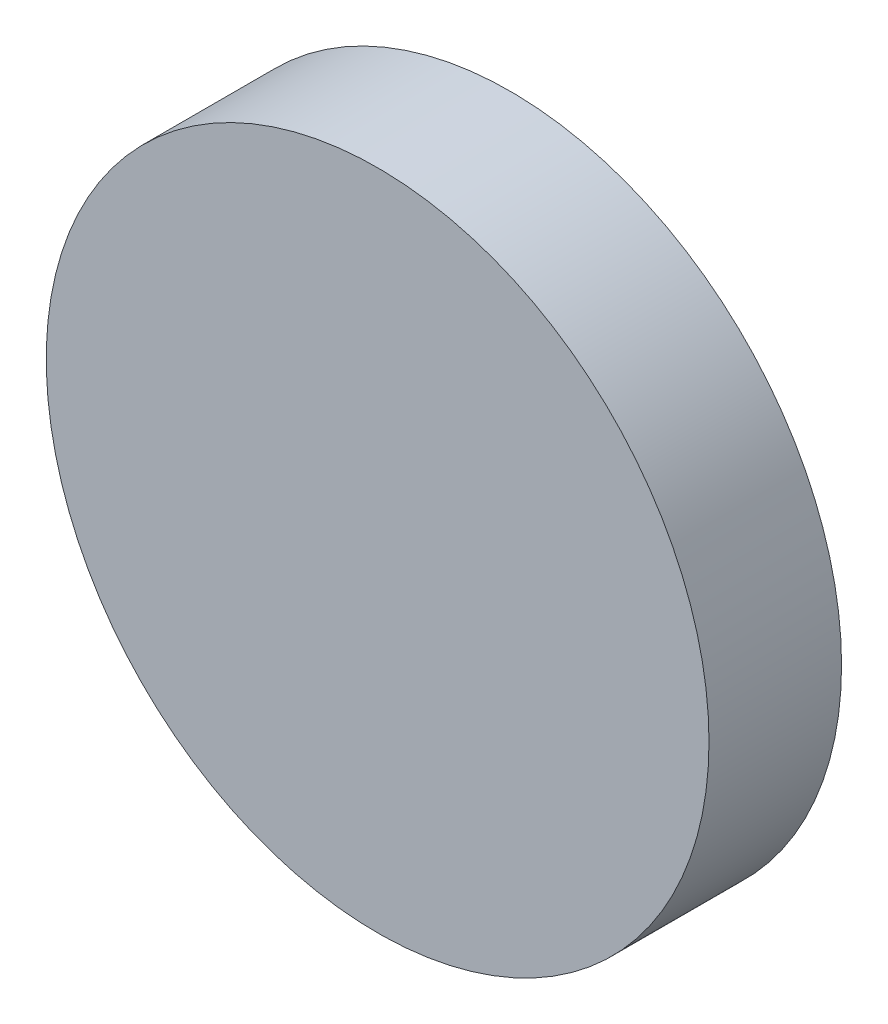
SolidWorks part; units mm, degrees
ref_plane "Front" through (0, 0, 0) normal (0, 0, 1) x (1, 0, 0)
ref_plane "Top" through (0, 0, 0) normal (0, 1, 0) x (1, 0, 0)
ref_plane "Right" through (0, 0, 0) normal (1, 0, 0) x (0, 0, -1)
sketch "Sketch1" plane through (0, 0, 0) normal (0, 0, 1) x (1, 0, 0)
  circle A0 centre (0, 0) radius 63.5
  dimension "D1" = 127
extrude "Extrude1" add sketch "Sketch1" along normal blind 25.4
